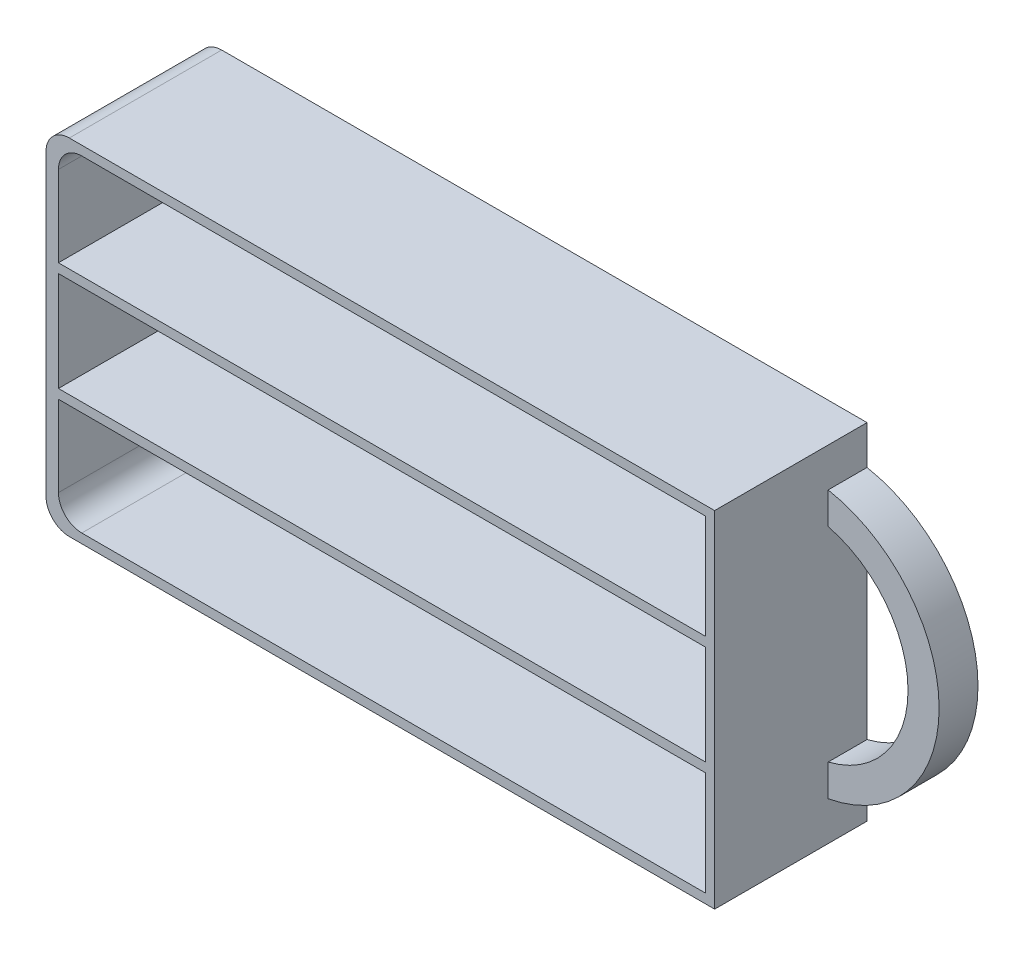
SolidWorks part; units mm, degrees
ref_plane "Спереди" through (0, 0, 0) normal (0, 0, 1) x (1, 0, 0)
ref_plane "Сверху" through (0, 0, 0) normal (0, 1, 0) x (1, 0, 0)
ref_plane "Справа" through (0, 0, 0) normal (1, 0, 0) x (0, 0, -1)
other "Configuration Table"
sketch "Эскиз1" plane through (0, 0, 0) normal (0, 0, 1) x (1, 0, 0)
  line L1 (-43, 22.2) -> (43, 22.2)
  line L2 (-43, 22.2) -> (-43, -22.2)
  line L3 (-43, -22.2) -> (43, -22.2)
  line L4 (43, 22.2) -> (43, -22.2)
  line L5 (-43, 22.2) -> (43, -22.2) construction
  line L6 (-43, -22.2) -> (43, 22.2) construction
  point P0 (0, 0)
  dimension "D1" = 86
  dimension "D2" = 44.4
extrude "Бобышка-Вытянуть1" add sketch "Эскиз1" along normal blind 19.6
sketch "Эскиз2" plane through (0, 0, 0) normal (0, 0, 1) x (1, 0, 0)
  line L0 (0, 0) -> (43, 0) construction
  line L1 (43, -22.2) -> (43, 22.2) construction
  line L2 (43, 17.2) -> (43, 13.1088)
  line L3 (43, -17.2) -> (43, -13.1088)
  arc A0 (43, -17.2) -> (43, 17.2) centre (39.7735, 0) ccw
  arc A1 (43, -13.1088) -> (43, 13.1088) centre (39.7735, 0) ccw
  dimension "D3" = 13.5
  dimension "D4" = 4
  dimension "D1" = 5
  dimension "D2" = 5
extrude "Бобышка-Вытянуть2" add sketch "Эскиз2" along normal blind 5
sketch "Эскиз3" plane through (0, 0, 19.6) normal (0, 0, 1) x (1, 0, 0)
  line L0 (0.2, -21) -> (0.2, 21) construction
  line L2 (41.8, 7.6) -> (-41.4, 7.6)
  line L3 (41.8, 7.6) -> (41.8, 6.4)
  line L4 (41.8, 6.4) -> (-41.4, 6.4)
  line L5 (-41.4, 22.2) -> (-41.4, -22.2)
  line L6 (-43, -21) -> (41.8, -21)
  line L7 (41.8, -21) -> (41.8, 21)
  line L8 (41.8, 21) -> (-43, 21)
  line L9 (-41.4, -21) -> (41.8, -21)
  line L10 (41.8, -21) -> (41.8, 21)
  line L11 (41.8, 21) -> (-41.4, 21)
  line L12 (-41.4, 21) -> (-41.4, -21)
  line L13 (-41.4, 7.6) -> (-41.4, 6.4)
  line L14 (41.8, 7.6) -> (-41.4, 6.4) construction
  line L15 (41.8, 6.4) -> (-41.4, 7.6) construction
  line L16 (41.8, -7.6) -> (-41.4, -7.6)
  line L17 (41.8, -7.6) -> (41.8, -6.4)
  line L18 (41.8, -6.4) -> (-41.4, -6.4)
  line L19 (-41.4, -7.6) -> (-41.4, -6.4)
  line L20 (41.8, -7.6) -> (-41.4, -6.4) construction
  line L21 (41.8, -6.4) -> (-41.4, -7.6) construction
  point P9 (0.2, 7)
  point P15 (0.2, -7)
  dimension "D3" = 1.2
  dimension "D4" = 1.2
  dimension "D5" = 42
  dimension "D6" = 14
  dimension "D7" = 14
  dimension "D8" = 14
  dimension "D1" = 1.2
  dimension "D2" = 1.6
extrude "Вырез-Вытянуть1" cut sketch "Эскиз3" against normal offset from surface (18.4 mm away) 1.2 contours L11 L12 L2 L10 | L18 L10 L4 L12 | L10 L16 L12 L9 up to face at (48.1368, 0, 0)
fillet "Скругление1" radius 3 4 edges at (-43, 22.2, 9.8) (-43, -22.2, 9.8) (-41.4, -21, 10.4) (-41.4, 21, 10.4)
equation "\"D4@Эскиз3\"=\"D3@Эскиз3\""
equation "\"D6@Эскиз3\"=(\"D5@Эскиз3\"/3)"
equation "\"D7@Эскиз3\"=\"D6@Эскиз3\""
